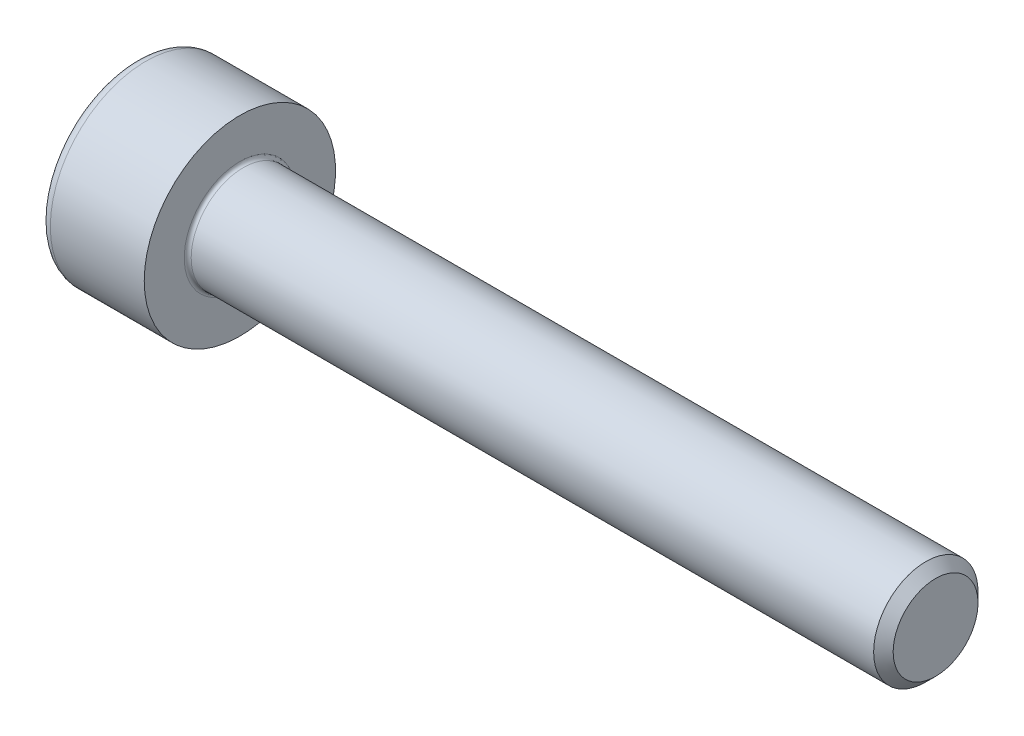
SolidWorks part; units mm, degrees
ref_plane "Plane1" through (0, 0, 0) normal (0, 0, 1) x (1, 0, 0)
ref_plane "Plane2" through (0, 0, 0) normal (0, 1, 0) x (1, 0, 0)
ref_plane "Plane3" through (0, 0, 0) normal (1, 0, 0) x (0, 0, -1)
sketch "BodySke" plane through (0, 0, 0) normal (0, 0, 1) x (1, 0, 0)
  line L0 (0, 0) -> (0, 2.75)
  line L1 (0, 2.75) -> (3, 2.75)
  line L2 (3, 2.75) -> (3, 1.5)
  line L3 (3, 1.5) -> (22.7195, 1.5)
  line L4 (23, 1.2195) -> (23, 0)
  line L5 (23, 0) -> (0, 0)
  line L6 (-31.75, 0) -> (127, 0) construction
  line L8 (23, 1.2195) -> (22.7195, 1.5)
  line L10 (23, -1.2195) -> (22.7195, -1.5) construction
  line L11 (3.5, 9.525) -> (3.5, 3.175) construction
  line L12 (5, 9.525) -> (5, 3.175) construction
  line L13 (-37, 9.525) -> (-37, 3.175) construction
  dimension "Diameter" = 3
  dimension "Head_ht" = 3
  dimension "Length" = 20
  dimension "Body_ch_ang" = 45
  dimension "Head_dia" = 5.5
  dimension "Minor_dia" = 2.439
  dimension "Advance" = 0.5
  dimension "Thread_nom" = 18
  dimension "Thread_length" = 60
revolve "Base-Revolve" add sketch "BodySke"
cosmetic thread "ThreadCosmetic" [suppressed]
fillet "Fillet1" radius 0.1 1 edges at (3, 0, 1.5)
fillet "Fillet2" radius 0.3 1 edges at (0, 0, 2.75)
sketch "Sketch2" plane through (0, 0, 0) normal (0, 0, 1) x (1, 0, 0)
  line L0 (0, 1.26) -> (1.3, 1.26)
  line L1 (1.3, 1.26) -> (2.0275, 0)
  line L2 (-31.75, 0) -> (127, 0) construction
  line L3 (2.0275, 0) -> (0, 0)
  line L4 (0, 0) -> (0, 1.26)
  line L6 (0, 0) -> (47.625, 0) construction
  dimension "D1" = 1.26
  dimension "D2" = 60
  dimension "Depth" = 1.3
revolve "Hex-PreBroach" cut sketch "Sketch2" angle 360 about L6
sketch "Sketch3" plane through (0, 0, 0) normal (-1, 0, 0) x (0, 0.5, 0.866)
  line L0 (0.7275, 1.26) -> (-0.7275, 1.26)
  line L1 (-0.7275, 1.26) -> (-1.4549, 0)
  line L2 (0.7275, 1.26) -> (1.4549, 0)
  line L3 (0.7275, -1.26) -> (1.4549, 0)
  line L4 (0.7275, -1.26) -> (-0.7275, -1.26)
  line L5 (-0.7275, -1.26) -> (-1.4549, 0)
  dimension "D1" = 1.26
  dimension "D2" = 1.26
  dimension "Hex_size" = 2.52
extrude "Hex" cut sketch "Sketch3" against normal blind 1.3
sketch "ThdSchSke" plane through (0, 0, 0) normal (0, 0, 1) x (1, 0, 0)
  line L0 (5, -1.2195) -> (4.8036, -1.5)
  line L1 (5, -1.2195) -> (5.1964, -1.5)
  line L2 (5.1964, -1.5) -> (5.1964, -1.875)
  line L3 (-3.175, 0) -> (5.1513, 0) construction
  line L4 (0, 2.45) -> (0, -2.45) construction
  line L5 (5.1964, -1.875) -> (4.8036, -1.875)
  line L6 (4.8036, -1.875) -> (4.8036, -1.5)
  dimension "Thread_minor" = 2.439
  dimension "Diameter" = 3
  dimension "Start" = 5
  dimension "SideAngle" = 55
  dimension "VeeAngle" = 70
  dimension "Overcut" = 3.75
revolve "ThreadSchematic" [suppressed] cut sketch "ThdSchSke" angle 360 about L3
pattern_linear "ThdSchPat" [suppressed]
equation "\"D2@Sketch3\" = \"Hex_size@Sketch3\" / 2"
equation "\"D1@Sketch3\" = \"Hex_size@Sketch3\" / 2"
equation "\"D1@Sketch2\" = \"Hex_size@Sketch3\" / 2"
equation "\"Thread_minor@ThreadCosmetic\"  =  \"Minor_dia@BodySke\""
equation "\"Depth@Sketch2\" =  \"Key_eng@Hex\""
equation "\"Thread_length@ThreadCosmetic\" = ((sgn( (\"Length@BodySke\" - \"Advance@BodySke\" * 3.0) - \"Thread_nom@BodySke\" )-1)*( (\"Length@BodySke\" - \"Advance@BodySke\" * 3.0) - \"Thread_nom@BodySke\" ))/-2+ \"Thread_nom@BodySke\""
equation "\"Thread_minor@ThdSchSke\" = \"Minor_dia@BodySke\""
equation "\"Diameter@ThdSchSke\" = \"Diameter@BodySke\""
equation "\"Overcut@ThdSchSke\" = \"Diameter@BodySke\" * 1.25"
equation "\"Start@ThdSchSke\" = \"Head_ht@BodySke\" + \"Length@BodySke\" - \"Thread_length@ThreadCosmetic\"  '---Non-countersunk---"
equation "\"Num_threads@ThdSchPat\" = int( \"Thread_length@ThreadCosmetic\" / \"Advance@BodySke\" + 0.999 )  + 1"
equation "\"Advance@ThdSchPat\" = \"Thread_length@ThreadCosmetic\" /  (\"Num_threads@ThdSchPat\" - 1) 'relax it"
equation "\"Num_threads@ThdSchPat\" = \"Num_threads@ThdSchPat\" - sgn( \"Num_threads@ThdSchPat\" - 1) '---chamfered tips only---"
